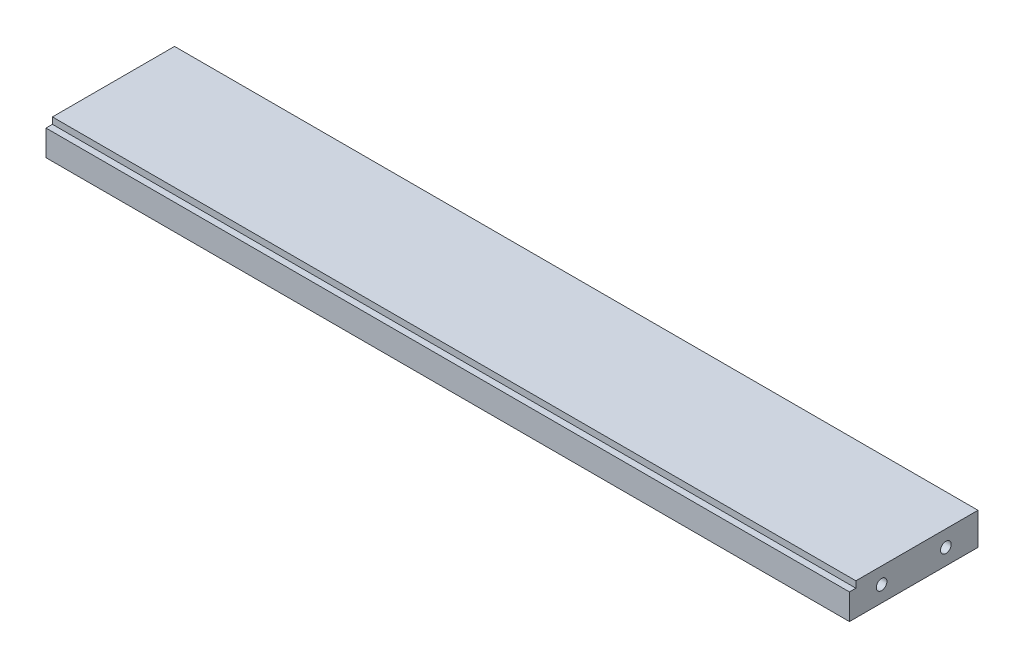
SolidWorks part; units mm, degrees
ref_plane "Front Plane" through (0, 0, 0) normal (0, 0, 1) x (1, 0, 0)
ref_plane "Top Plane" through (0, 0, 0) normal (0, 1, 0) x (1, 0, 0)
ref_plane "Right Plane" through (0, 0, 0) normal (1, 0, 0) x (0, 0, -1)
sketch "Sketch1" plane through (0, 0, 0) normal (0, 1, 0) x (1, 0, 0)
  line L1 (-125, -20) -> (125, -20)
  line L2 (-125, -20) -> (-125, 20)
  line L3 (-125, 20) -> (125, 20)
  line L4 (125, -20) -> (125, 20)
  line L5 (-125, -20) -> (125, 20) construction
  line L6 (-125, 20) -> (125, -20) construction
  point P0 (0, 0)
  dimension "D1" = 40
  dimension "D2" = 250
extrude "Boss-Extrude1" add sketch "Sketch1" along normal mid plane 10
sketch "Sketch5" plane through (0, 0, 0) normal (1, 0, 0) x (0, 0, -1)
  line L0 (-20, 5) -> (20, 5) construction
  line L1 (-20, 5) -> (-18, 5)
  line L2 (-20, 5) -> (-20, 3)
  line L3 (-20, 3) -> (-18, 3)
  line L4 (-18, 5) -> (-18, 3)
  line L5 (-20, 5) -> (-20, -5) construction
  dimension "D1" = 2
  dimension "D2" = 2
extrude "Cut-Extrude2" cut sketch "Sketch5" against normal through all both and the other way through all
hole_wizard "M4 Tapped Hole1" positions "Sketch6" profile "Sketch8" tap size "M4" standard "DIN"
sketch "Sketch6" plane through (125, 0, 0) normal (1, 0, 0) x (0, 0, -1)
  line L0 (22, 0) -> (-22, 0) construction
  line L1 (0, 5.5) -> (0, -5.5) construction
  point P0 (10, 0)
  point P2 (-10, 0)
  dimension "D1" = 10
  dimension "D2" = 10
sketch "Sketch8" plane through (125, 0, -10) normal (0, 1, 0) x (0, 0, -1)
  line L0 (0, 0) -> (0, 14.9914)
  line L1 (0, 14.9914) -> (1.65, 14)
  line L2 (1.65, 14) -> (1.65, 0)
  line L5 (1.65, 0) -> (0, 0)
  line L10 (0, 14.9914) -> (-1.65, 14) construction
  line L11 (0, -6.35) -> (0, 107.95) construction
  dimension "Tap Drill Dia." = 3.3
  dimension "Tap Drill Depth" = 14
  dimension "Drill Angle" = 118
cosmetic thread "Hole Thread3" parameters "D1"=12, "D2"=4
cosmetic thread "Hole Thread4" parameters "D1"=12, "D2"=4
mirror "Mirror1" about plane through (0, 0, 0) normal (1, 0, 0) of "M4 Tapped Hole1"
hole_wizard "M4x0.7 Tapped Hole1" positions "Sketch9" profile "Sketch10" tap size "M4x0.7" standard "ANSI Metric"
sketch "Sketch9" plane through (0, 0, -20) normal (0, 0, -1) x (-1, 0, 0)
  line L0 (22, 0) -> (-22, 0) construction
  line L1 (0, 5.5) -> (0, -5.5) construction
  point P0 (-75, 0)
  point P2 (75, 0)
  dimension "D1" = 75
  dimension "D2" = 75
sketch "Sketch10" plane through (75, 0, -20) normal (1, 0, 0) x (0, 1, 0)
  line L0 (0, 0) -> (0, 14.9914)
  line L1 (0, 14.9914) -> (1.65, 14)
  line L2 (1.65, 14) -> (1.65, 0)
  line L5 (1.65, 0) -> (0, 0)
  line L10 (0, 14.9914) -> (-1.65, 14) construction
  line L11 (0, -6.35) -> (0, 107.95) construction
  dimension "Tap Drill Dia." = 3.3
  dimension "Tap Drill Depth" = 14
  dimension "Drill Angle" = 118
cosmetic thread "Hole Thread5" parameters "D1"=12, "D2"=4
cosmetic thread "Hole Thread6" parameters "D1"=12, "D2"=4
